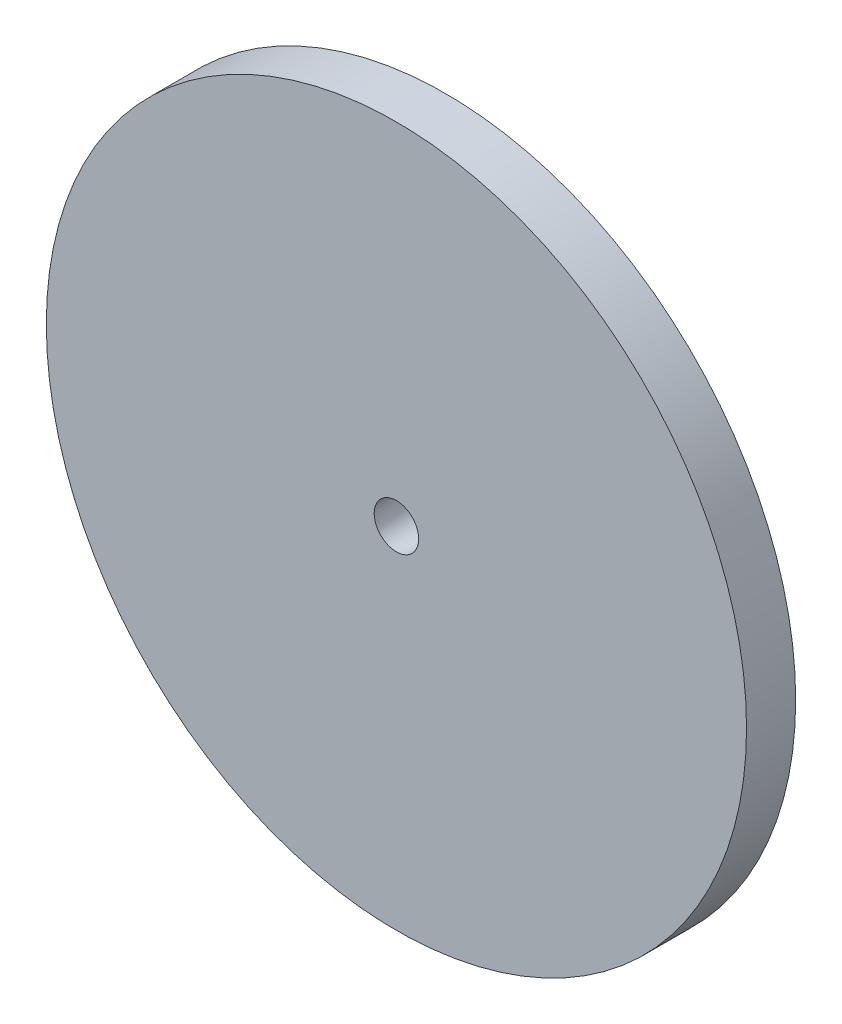
SolidWorks part; units mm, degrees
ref_plane "Front Plane" through (0, 0, 0) normal (0, 0, 1) x (1, 0, 0)
ref_plane "Top Plane" through (0, 0, 0) normal (0, 1, 0) x (1, 0, 0)
ref_plane "Right Plane" through (0, 0, 0) normal (1, 0, 0) x (0, 0, -1)
sketch "Sketch1" plane through (0, 0, 0) normal (0, 0, 1) x (1, 0, 0)
  circle A0 centre (0, 0) radius 38.0001
  dimension "D1" = 76.0001
extrude "Boss-Extrude1" add sketch "Sketch1" along normal blind 5.334
sketch "Sketch2" plane through (0, 0, 5.334) normal (0, 0, 1) x (1, 0, 0)
  circle A0 centre (0, 0) radius 2.413
  dimension "D1" = 4.826
extrude "Cut-Extrude1" cut sketch "Sketch2" against normal through all
equation "\"GMaterial\" = 0.21in"
equation "\"MDF\"= 0.21in"
equation "\"Foamcore\"= 0.2in"
equation "\"D1@Boss-Extrude1\"=\"GMaterial\""
